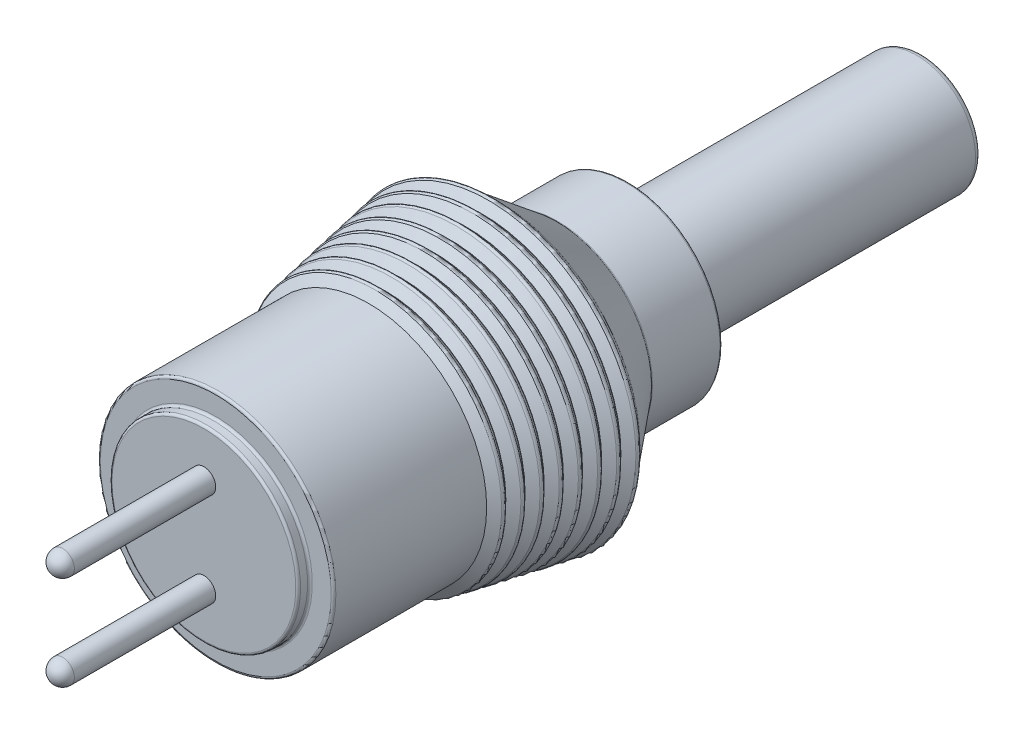
SolidWorks part; units mm, degrees
ref_plane "Front" through (0, 0, 0) normal (0, 0, 1) x (1, 0, 0)
ref_plane "Top" through (0, 0, 0) normal (0, 1, 0) x (1, 0, 0)
ref_plane "Right" through (0, 0, 0) normal (1, 0, 0) x (0, 0, -1)
sketch "Sketch1" plane through (0, 0, 0) normal (1, 0, 0) x (0, 0, -1)
  line L0 (-15.25, 0) -> (15.25, 0)
  line L1 (2.75, 4) -> (2.75, 2.5)
  line L2 (-14.75, 5) -> (-8.25, 5)
  line L3 (-15.25, 0) -> (-15.25, 4)
  line L4 (-7.5728, 5.1231) -> (-7.5612, 5.1252)
  line L5 (-0.25, 4) -> (2.75, 4)
  line L6 (-2.75, 6) -> (-0.25, 4)
  line L7 (2.75, 2.5) -> (15.25, 2.5)
  line L8 (15.25, 2.5) -> (15.25, 0)
  line L9 (-8.25, 5) -> (-7.9223, 5.4789)
  line L10 (-7.9223, 5.4789) -> (-7.5728, 5.1231)
  line L11 (-7.2335, 5.6041) -> (-6.8842, 5.2483)
  line L12 (-7.5612, 5.1252) -> (-7.2335, 5.6041)
  line L13 (-6.5448, 5.7292) -> (-6.1955, 5.3735)
  line L14 (-6.8725, 5.2505) -> (-6.5448, 5.7292)
  line L15 (-5.8561, 5.8544) -> (-5.5068, 5.4988)
  line L16 (-6.1837, 5.3757) -> (-5.8561, 5.8544)
  line L17 (-5.1674, 5.9796) -> (-4.818, 5.6238)
  line L18 (-5.4949, 5.5009) -> (-5.1674, 5.9796)
  line L19 (-4.4787, 6.1047) -> (-4.1295, 5.7492)
  line L20 (-4.8064, 5.6258) -> (-4.4787, 6.1047)
  line L21 (-3.7899, 6.2299) -> (-3.4408, 5.8744)
  line L22 (-4.1174, 5.7514) -> (-3.7899, 6.2299)
  line L23 (-3.1012, 6.3551) -> (-2.7522, 5.9996)
  line L24 (-3.4286, 5.8766) -> (-3.1012, 6.3551)
  line L25 (-6.8842, 5.2483) -> (-6.8725, 5.2505)
  line L26 (-6.1955, 5.3735) -> (-6.1837, 5.3757)
  line L27 (-5.5068, 5.4988) -> (-5.4949, 5.5009)
  line L28 (-4.1295, 5.7492) -> (-4.1174, 5.7514)
  line L29 (-3.4408, 5.8744) -> (-3.4286, 5.8766)
  line L30 (-2.7522, 5.9996) -> (-2.75, 6)
  line L31 (-15.25, 4) -> (-14.75, 4)
  line L32 (-14.75, 4) -> (-14.75, 5)
  line L33 (-4.818, 5.6238) -> (-4.8064, 5.6258)
  line L34 (-7.2335, 5.6041) -> (-6.8841, 5.2483) [skipped]
  point P7 (-2.75, 6)
  dimension "D1" = 30.5
  dimension "D2" = 18
  dimension "D3" = 5
  dimension "D4" = 6
  dimension "D5" = 12.5
  dimension "D7" = 3
  dimension "D8" = 4
  dimension "D9" = 2.5
  dimension "D10" = 8
  dimension "D11" = 0.5
revolve "Revolve1" add sketch "Sketch1" angle 360 about L0
sketch "Sketch2" plane through (0, 0, -15.25) normal (0, 0, -1) x (-1, 0, 0)
  circle A0 centre (0, 0) radius 1.75
  dimension "D1" = 3.5
extrude "Cut-Extrude1" cut sketch "Sketch2" against normal blind 12
fillet "Fillet1" radius 0.1 8 edges at (6.3551, 0, 3.1012) (6.2299, 0, 3.7899) (6.1047, 0, 4.4787) (5.9796, 0, 5.1674) (5.8544, 0, 5.8561) (5.7292, 0, 6.5448) (5.6041, 0, 7.2335) (5.4789, 0, 7.9223)
fillet "Fillet2" radius 0.25 1 edges at (2.5, 0, -15.25)
fillet "Fillet3" radius 0.1 6 edges at (4, 0, 15.25) (4, 0, 14.75) (5, 0, 14.75) (4, 0, 0.25) (2.5, 0, -2.75) (4, 0, -2.75)
sketch "Sketch3" plane through (0, 0, 15.25) normal (0, 0, 1) x (1, 0, 0)
  circle A0 centre (0, 2) radius 0.5
  circle A1 centre (0, -2) radius 0.5
  dimension "D1" = 1
  dimension "D2" = 2
  dimension "D3" = 2
extrude "Boss-Extrude1" add sketch "Sketch3" along normal blind 6.5
fillet "Fillet4" radius 0.5 2 edges at (0.5, -2, 21.75) (0.5, 2, 21.75)
